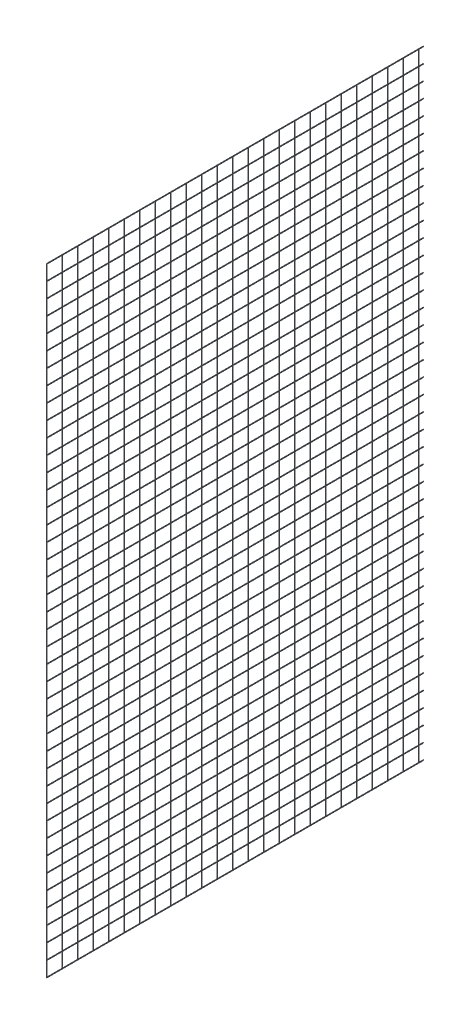
SolidWorks part; units mm, degrees
material "1.0570 (S355J2G3)"
ref_plane "Top Plane" through (0, 0, 0) normal (0, 0, 1) x (1, 0, 0)
ref_plane "Right Plane" through (0, 0, 0) normal (0, 1, 0) x (1, 0, 0)
ref_plane "Front Plane" through (0, 0, 0) normal (1, 0, 0) x (0, 0, -1)
sketch "Sketch1" plane through (0, 0, 0) normal (0, 1, 0) x (1, 0, 0)
  line L0 (0, 0) -> (0, 2000)
  dimension "D1" = 2000
sketch "Sketch2" plane through (0, 0, 0) normal (0, 0, 1) x (1, 0, 0)
  circle A0 centre (0, 0) radius 1.5
  dimension "D1" = 3
sweep "Sweep2" add profiles "Sketch2" path "Sketch1"
pattern_linear "LPattern3" count 42 spacing 80 along (0, 1, 0) of bodies 102
sketch "Sketch9" plane through (0, 0, 0) normal (1, 0, 0) x (0, 0, -1)
  line L0 (1.5, 3280) -> (1.5, 0)
  line L4 (0, -1.5) -> (2000, -1.5) construction
  line L5 (2000, 3281.5) -> (0, 3281.5) construction
  line L6 (0, 3281.5) -> (0, 3278.5) construction
  point P2 (0, 0)
  dimension "D1" = 1.5
  dimension "D2" = 1.5
  dimension "D3" = 1.5
sketch "Sketch10" plane through (0, 0, 0) normal (0, 1, 0) x (1, 0, 0)
  circle A0 centre (0, 1.5) radius 1.5
  dimension "D1" = 3
sweep "Sweep3" add profiles "Sketch10" path "Sketch9"
pattern_linear "LPattern4" count 25 spacing 82.24 along (0, 0, -1) of "Sweep3"
